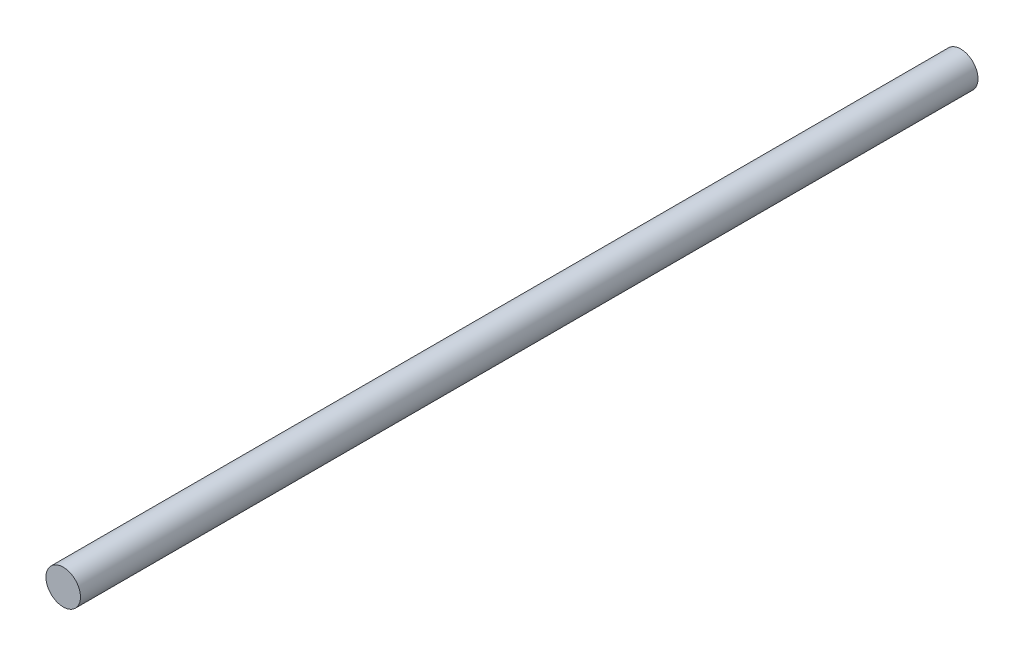
SolidWorks part; units mm, degrees
ref_plane "Front" through (0, 0, 0) normal (0, 0, 1) x (1, 0, 0)
ref_plane "Top" through (0, 0, 0) normal (0, 1, 0) x (1, 0, 0)
ref_plane "Right" through (0, 0, 0) normal (1, 0, 0) x (0, 0, -1)
sketch "Sketch1" plane through (0, 0, 0) normal (0, 0, 1) x (1, 0, 0)
  circle A0 centre (0, 0) radius 2
  dimension "D1" = 4
extrude "Boss-Extrude1" add sketch "Sketch1" along normal blind 104
